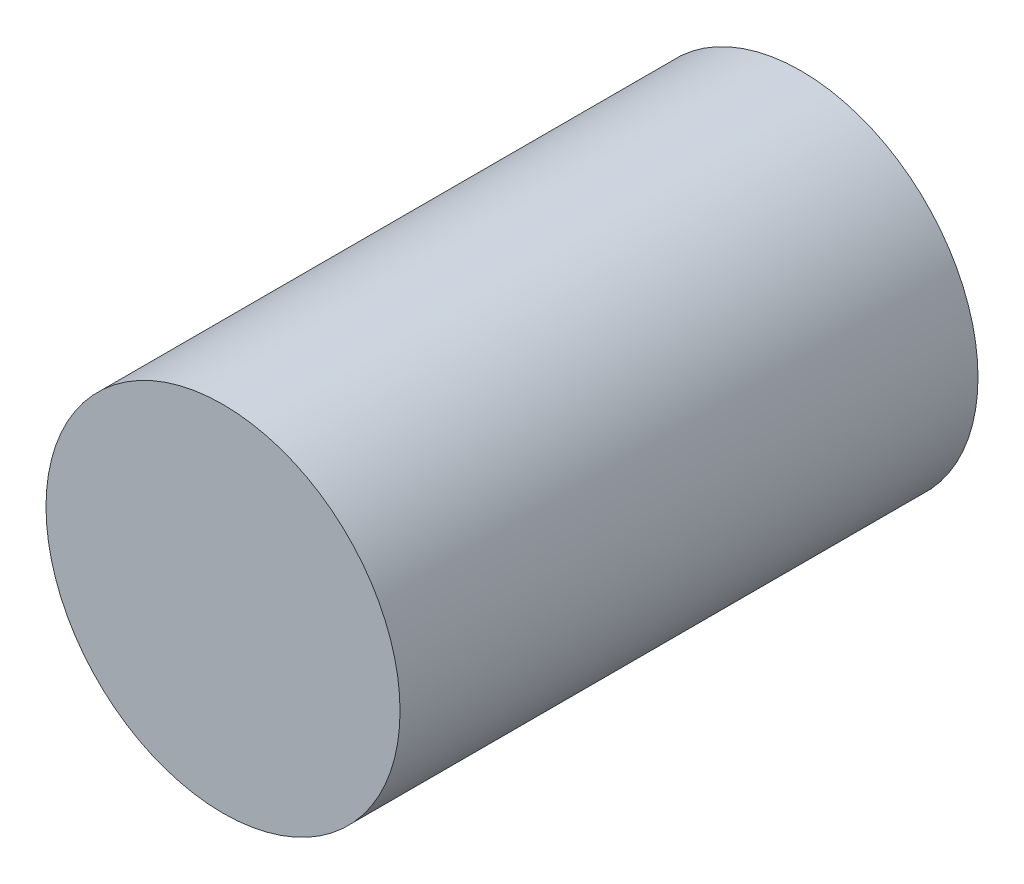
SolidWorks part; units mm, degrees
ref_plane "Front Plane" through (0, 0, 0) normal (0, 0, 1) x (1, 0, 0)
ref_plane "Top Plane" through (0, 0, 0) normal (0, 1, 0) x (1, 0, 0)
ref_plane "Right Plane" through (0, 0, 0) normal (1, 0, 0) x (0, 0, -1)
sketch "Sketch2" plane through (0, 0, 0) normal (0, 0, 1) x (1, 0, 0)
  circle A0 centre (15, 15) radius 6.425
extrude "Boss-Extrude1" add sketch "Sketch2" along normal blind 6.45 and the other way blind 14.5271
